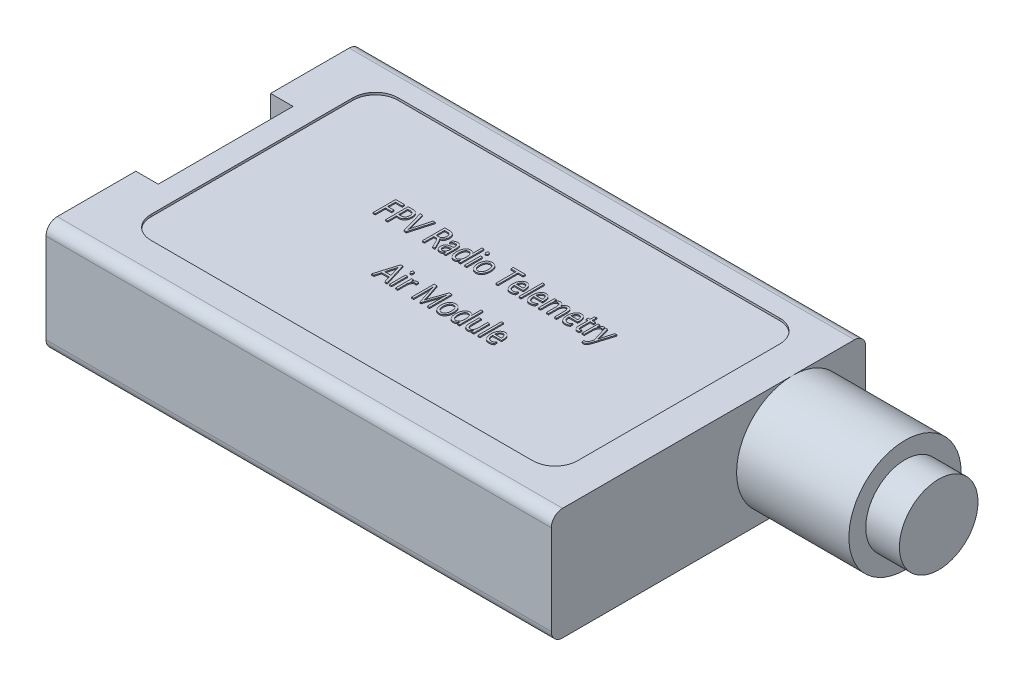
SolidWorks part; units mm, degrees
ref_plane "Front Plane" through (0, 0, 0) normal (0, 0, 1) x (1, 0, 0)
ref_plane "Top Plane" through (0, 0, 0) normal (0, 1, 0) x (1, 0, 0)
ref_plane "Right Plane" through (0, 0, 0) normal (1, 0, 0) x (0, 0, -1)
sketch "Sketch1" plane through (0, 0, 0) normal (0, 1, 0) x (1, 0, 0)
  line L1 (-22.5, -14) -> (22.5, -14)
  line L2 (-22.5, -14) -> (-22.5, 14)
  line L3 (-22.5, 14) -> (22.5, 14)
  line L4 (22.5, -14) -> (22.5, 14)
  line L5 (-22.5, -14) -> (22.5, 14) construction
  line L6 (-22.5, 14) -> (22.5, -14) construction
  point P0 (0, 0)
  dimension "D1" = 45
  dimension "D2" = 28
extrude "Boss-Extrude1" add sketch "Sketch1" along normal blind 10
fillet "Fillet1" radius 1 4 edges at (0, 0, -14) (0, 0, 14) (0, 10, -14) (0, 10, 14)
sketch "Sketch2" plane through (0, 10, 0) normal (0, 1, 0) x (1, 0, 0)
  line L1 (-20.5, -6) -> (-22.5, -6)
  line L2 (-20.5, -6) -> (-20.5, 6)
  line L3 (-20.5, 6) -> (-22.5, 6)
  line L4 (-22.5, -6) -> (-22.5, 6)
  line L5 (-20.5, -6) -> (-22.5, 6) construction
  line L6 (-20.5, 6) -> (-22.5, -6) construction
  point P0 (-21.5, 0)
  dimension "D1" = 12
  dimension "D2" = 2
extrude "Cut-Extrude1" cut sketch "Sketch2" against normal blind 5
sketch "Sketch3" plane through (-20.5, 0, 0) normal (-1, 0, 0) x (0, 0, 1)
  line L0 (6, 5) -> (-6, 5) construction
  line L1 (-4.8892, 8) -> (5.1108, 8)
  line L2 (-4.8892, 8) -> (-4.8892, 5)
  line L3 (-4.8892, 5) -> (5.1108, 5)
  line L4 (5.1108, 8) -> (5.1108, 5)
  line L5 (-4.8892, 8) -> (5.1108, 5) construction
  line L6 (-4.8892, 5) -> (5.1108, 8) construction
  point P0 (0.1108, 6.5)
  dimension "D1" = 10
  dimension "D2" = 3
extrude "Boss-Extrude3" add sketch "Sketch3" along normal blind 1 contours L1 L4 L3 L2
sketch "Sketch4" plane through (-21.5, 0, 0) normal (-1, 0, 0) x (0, 0, 1)
  line L1 (-4.4906, 7.5637) -> (4.6906, 7.5637)
  line L2 (-4.4906, 7.5637) -> (-4.4906, 5.4363)
  line L3 (-4.4906, 5.4363) -> (4.6906, 5.4363)
  line L4 (4.6906, 7.5637) -> (4.6906, 5.4363)
  line L5 (-4.4906, 7.5637) -> (4.6906, 5.4363) construction
  line L6 (-4.4906, 5.4363) -> (4.6906, 7.5637) construction
  point P0 (0.1, 6.5)
extrude "Cut-Extrude2" cut sketch "Sketch4" against normal blind 1
sketch "Sketch7" plane through (-20.5, 0, 0) normal (-1, 0, 0) x (0, 0, 1)
  line L0 (1.75, 6.7) -> (2.25, 6.7)
  line L1 (0.4167, 6.7) -> (0.9167, 6.7)
  line L2 (0.4167, 6.7) -> (0.4167, 5.7)
  line L3 (0.4167, 5.7) -> (0.9167, 5.7)
  line L4 (0.9167, 6.7) -> (0.9167, 5.7)
  line L5 (0.4167, 6.7) -> (0.9167, 5.7) construction
  line L6 (0.4167, 5.7) -> (0.9167, 6.7) construction
  line L7 (1.75, 6.7) -> (1.75, 5.7)
  line L8 (1.75, 5.7) -> (2.25, 5.7)
  line L9 (2.25, 6.7) -> (2.25, 5.7)
  line L10 (1.75, 6.7) -> (2.25, 5.7) construction
  line L11 (1.75, 5.7) -> (2.25, 6.7) construction
  line L12 (-2.25, 6.7) -> (-1.75, 6.7)
  line L13 (-0.9167, 6.7) -> (-0.4167, 6.7)
  line L14 (-0.9167, 6.7) -> (-0.9167, 5.7)
  line L15 (-0.9167, 5.7) -> (-0.4167, 5.7)
  line L16 (-0.4167, 6.7) -> (-0.4167, 5.7)
  line L17 (-0.9167, 6.7) -> (-0.4167, 5.7) construction
  line L18 (-0.9167, 5.7) -> (-0.4167, 6.7) construction
  line L19 (-2.25, 6.7) -> (-2.25, 5.7)
  line L20 (-2.25, 5.7) -> (-1.75, 5.7)
  line L21 (-1.75, 6.7) -> (-1.75, 5.7)
  line L22 (-2.25, 6.7) -> (-1.75, 5.7) construction
  line L23 (-2.25, 5.7) -> (-1.75, 6.7) construction
  point P0 (0.6667, 6.2)
  point P5 (2, 6.2)
  point P10 (-0.6667, 6.2)
  point P15 (-2, 6.2)
  dimension "D1" = 1
  dimension "D2" = 0.5
  dimension "D3" = 1
extrude "Boss-Extrude4" add sketch "Sketch7" along normal blind 2
chamfer "Chamfer1" distance 0.1 angle 70 16 edges at (-22.5, 5.7, -2) (-22.5, 6.2, -2.25) (-22.5, 6.7, -2) (-22.5, 6.2, -1.75) (-22.5, 5.7, 2) (-22.5, 6.2, 1.75) (-22.5, 6.7, 2) (-22.5, 6.2, 2.25) (-22.5, 5.7, 0.6667) (-22.5, 6.2, 0.4167) (-22.5, 6.7, 0.6667) (-22.5, 6.2, 0.9167) (-22.5, 5.7, -0.6667) (-22.5, 6.2, -0.9167) (-22.5, 6.7, -0.6667) (-22.5, 6.2, -0.4167)
sketch "Sketch8" plane through (0, 10, 0) normal (0, 1, 0) x (1, 0, 0)
  line L0 (22.5, -13) -> (22.5, 13) construction
  line L1 (17.5, -10.6566) -> (-16.5, -10.6566)
  line L2 (19.5, -8.6566) -> (19.5, 9.3434)
  line L3 (17.5, 11.3434) -> (-16.5, 11.3434)
  line L4 (-18.5, -8.6566) -> (-18.5, 9.3434)
  arc A0 (19.5, 9.3434) -> (17.5, 11.3434) centre (17.5, 9.3434) ccw
  arc A1 (-16.5, 11.3434) -> (-18.5, 9.3434) centre (-16.5, 9.3434) ccw
  arc A2 (-16.5, -10.6566) -> (-18.5, -8.6566) centre (-16.5, -8.6566) cw
  arc A3 (17.5, -10.6566) -> (19.5, -8.6566) centre (17.5, -8.6566) ccw
  point P8 (19.5, 11.3434)
  point P11 (-18.5, 11.3434)
  point P16 (19.5, -10.6566)
  dimension "D4" = 2
  dimension "D1" = 38
  dimension "D2" = 22
  dimension "D3" = 3
extrude "Cut-Extrude3" cut sketch "Sketch8" against normal blind 0.2
sketch "Sketch9" plane through (0, 9.8, 0) normal (0, 1, 0) x (1, 0, 0)
  text T0 "FPV Radio Telemetry\r\n        Air Module" font "Segoe UI" height 2
sketch "Sketch10" plane through (22.5, 0, 0) normal (1, 0, 0) x (0, 0, -1)
  circle A0 centre (7.5, 5) radius 5
extrude "Boss-Extrude5" add sketch "Sketch10" along normal blind 13
sketch "Sketch11" plane through (35.5, 0, 0) normal (1, 0, 0) x (0, 0, -1)
  circle A0 centre (7.5, 5) radius 3.5
extrude "Cut-Extrude4" cut sketch "Sketch11" against normal blind 3 flip side to cut
extrude "Boss-Extrude6" add sketch "Sketch9" along normal blind 0.1
